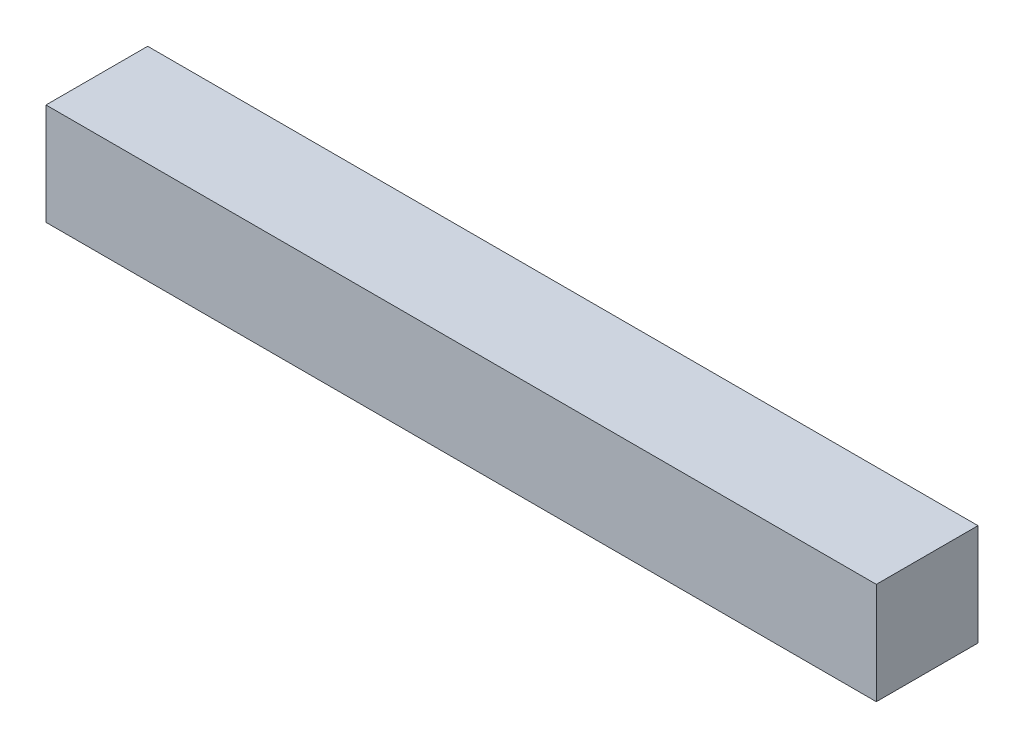
SolidWorks part; units mm, degrees
material "AISI 304"
ref_plane "Front Plane" through (0, 0, 0) normal (0, 0, 1) x (1, 0, 0)
ref_plane "Top Plane" through (0, 0, 0) normal (0, 1, 0) x (1, 0, 0)
ref_plane "Right Plane" through (0, 0, 0) normal (1, 0, 0) x (0, 0, -1)
sketch "Sketch1" plane through (0, 0, 0) normal (0, 1, 0) x (1, 0, 0)
  line L1 (0, 0) -> (24.5, 0)
  line L2 (0, 0) -> (0, 3)
  line L3 (0, 3) -> (24.5, 3)
  line L4 (24.5, 0) -> (24.5, 3)
  dimension "D1" = 24.5
  dimension "D2" = 3
extrude "Boss-Extrude1" add sketch "Sketch1" along normal blind 3
